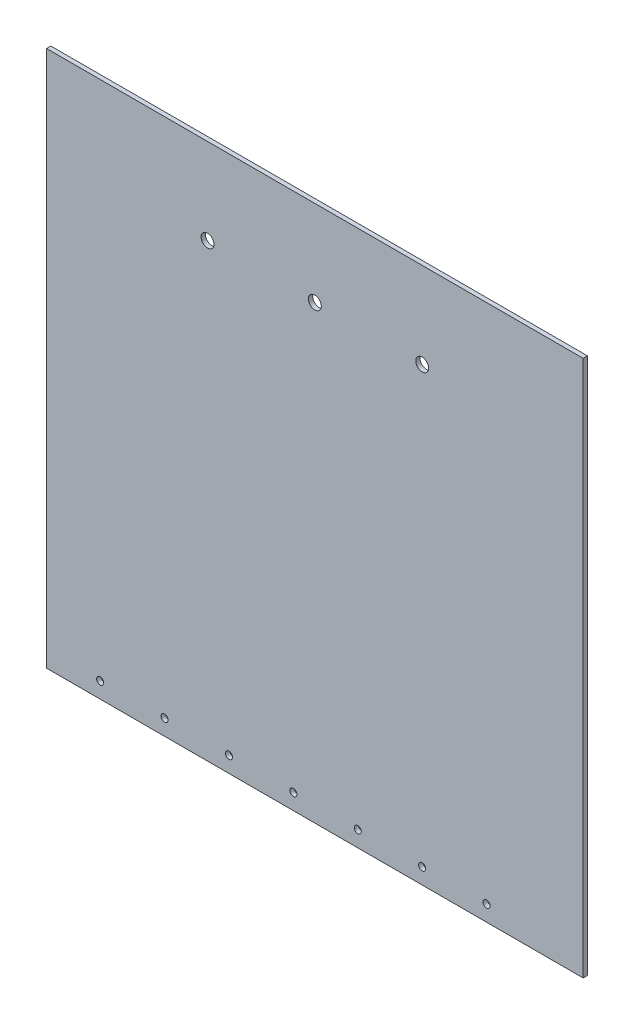
SolidWorks part; units mm, degrees
material "1060 Legierung"
ref_plane "Ebene vorne" through (0, 0, 0) normal (0, 0, 1) x (1, 0, 0)
ref_plane "Ebene oben" through (0, 0, 0) normal (0, 1, 0) x (1, 0, 0)
ref_plane "Ebene rechts" through (0, 0, 0) normal (1, 0, 0) x (0, 0, -1)
sketch "Skizze1" plane through (0, 0, 0) normal (0, 0, 1) x (1, 0, 0)
  line L1 (-125, -125) -> (125, -125)
  line L2 (-125, -125) -> (-125, 125)
  line L3 (-125, 125) -> (125, 125)
  line L4 (125, -125) -> (125, 125)
  point P7 (0, 125)
  point P8 (125, 0)
  dimension "D1" = 250
  dimension "D2" = 250
extrude "Aufsatz-Linear austragen1" add sketch "Skizze1" along normal blind 2
sketch "Skizze2" plane through (0, 0, 2) normal (0, 0, 1) x (1, 0, 0)
  line L0 (0, 0) -> (0, 85) construction
  line L1 (125, 125) -> (-125, 125) construction
  circle A0 centre (0, 85) radius 3
  circle A1 centre (-50, 85) radius 3
  circle A2 centre (50, 85) radius 3
  dimension "D1" = 6
  dimension "D2" = 50
  dimension "D3" = 40
extrude "Schnitt-Linear austragen1" cut sketch "Skizze2" against normal through all
hole_wizard "M4 Gewindebohrung1" positions "Skizze5" profile "Skizze6" tap size "M4" standard "DIN" end condition through all
sketch "Skizze5" plane through (0, 0, 0) normal (0, 0, -1) x (-1, 0, 0)
  line L0 (125, -125) -> (-125, -125) construction
  line L2 (125, 125) -> (125, -125) construction
  point P0 (-80, -117.64)
  point P9 (-50, -117.64)
  point P10 (-20, -117.64)
  point P11 (10, -117.64)
  point P12 (40, -117.64)
  point P13 (70, -117.64)
  point P14 (100, -117.64)
  point P15 (0, 0)
  point P17 (0, 0)
  dimension "D1" = 7.36
  dimension "D3" = 25
  dimension "D2" = 7
sketch "Skizze6" plane through (80, -117.64, 0) normal (1, 0, 0) x (0, 1, 0)
  line L0 (0, 0) -> (0, 2)
  line L1 (0, 2) -> (1.65, 2)
  line L2 (1.65, 2) -> (1.65, 0)
  line L5 (1.65, 0) -> (0, 0)
  line L11 (0, -6.35) -> (0, 107.95) construction
  dimension "Bohrerdurchmesser" = 3.3
  dimension "Bohrungstiefe" = 2
cosmetic thread "Bohrungsgewinde1" parameters "D2"=4
cosmetic thread "Bohrungsgewinde2" parameters "D2"=4
cosmetic thread "Bohrungsgewinde3" parameters "D2"=4
cosmetic thread "Bohrungsgewinde4" parameters "D2"=4
cosmetic thread "Bohrungsgewinde5" parameters "D2"=4
cosmetic thread "Bohrungsgewinde6" parameters "D2"=4
cosmetic thread "Bohrungsgewinde7" parameters "D2"=4
